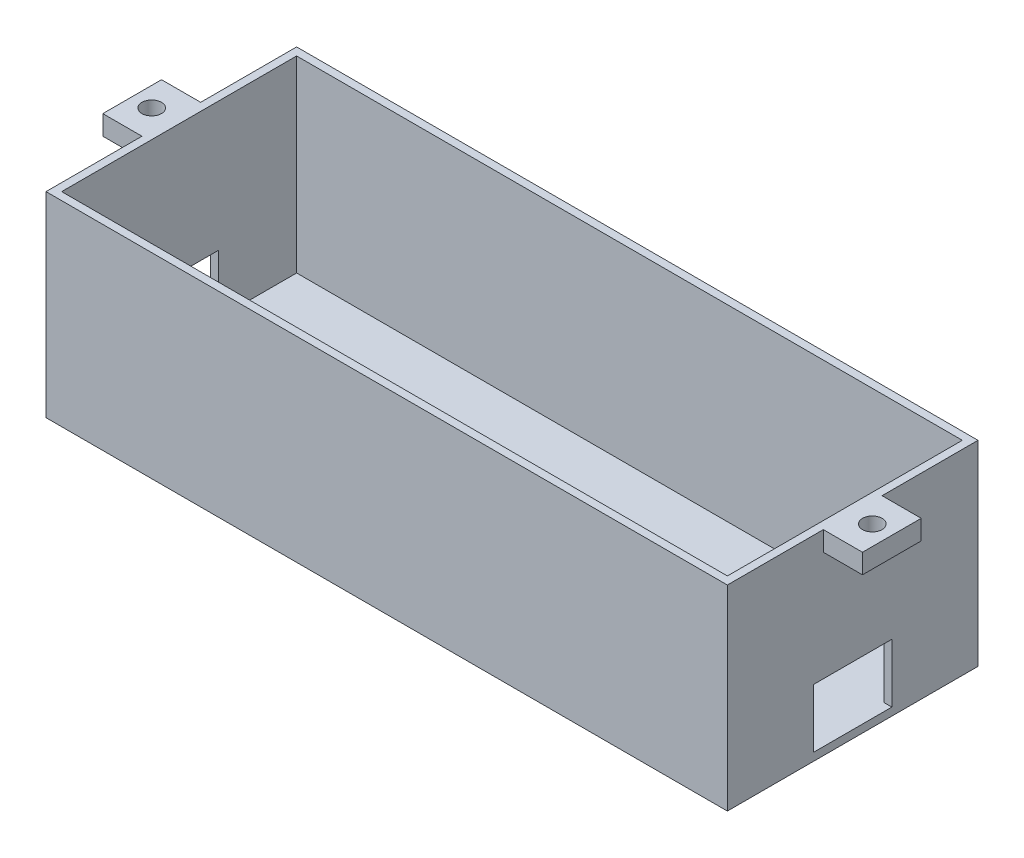
SolidWorks part; units mm, degrees
ref_plane "Front Plane" through (0, 0, 0) normal (0, 0, 1) x (1, 0, 0)
ref_plane "Top Plane" through (0, 0, 0) normal (0, 1, 0) x (1, 0, 0)
ref_plane "Right Plane" through (0, 0, 0) normal (1, 0, 0) x (0, 0, -1)
sketch "Sketch1" plane through (0, 0, 0) normal (0, 1, 0) x (1, 0, 0)
  line L1 (-85, -30) -> (85, -30)
  line L2 (-85, -30) -> (-85, 30)
  line L3 (-85, 30) -> (85, 30)
  line L4 (85, -30) -> (85, 30)
  line L5 (-85, -30) -> (85, 30) construction
  line L6 (-85, 30) -> (85, -30) construction
  line L7 (-87, -32) -> (87, -32)
  line L8 (-87, -32) -> (-87, 32)
  line L9 (-87, 32) -> (87, 32)
  line L10 (87, -32) -> (87, 32)
  line L11 (-87, -32) -> (87, 32) construction
  line L12 (-87, 32) -> (87, -32) construction
  point P0 (0, 0)
  point P6 (0, 0)
  dimension "D1" = 170
  dimension "D2" = 60
  dimension "D3" = 2
  dimension "D4" = 2
extrude "Boss-Extrude1" add sketch "Sketch1" along normal mid plane 50
sketch "Sketch2" plane through (0, 0, -32) normal (0, 0, -1) x (-1, 0, 0)
  line L0 (87, 25) -> (87, -25) construction
  line L1 (-87, -25) -> (87, -25)
  line L2 (-87, -25) -> (-87, -23)
  line L3 (-87, -23) -> (87, -23)
  line L4 (87, -25) -> (87, -23)
  dimension "D1" = 2
extrude "Boss-Extrude2" add sketch "Sketch2" against normal up to surface (64 mm away) up to face at (0, 0, 32)
sketch "Sketch9" plane through (0, 25, 0) normal (0, 1, 0) x (1, 0, 0)
  line L0 (-87, 32) -> (-87, -32) construction
  line L1 (-87, 7.5) -> (-97, 7.5)
  line L2 (-87, 7.5) -> (-87, -7.5)
  line L3 (-87, -7.5) -> (-97, -7.5)
  line L4 (-97, 7.5) -> (-97, -7.5)
  line L5 (0, 30) -> (0, -30)
  line L6 (85, 30) -> (-85, 30) construction
  line L7 (-85, -30) -> (85, -30) construction
  line L13 (87, -7.5) -> (97, -7.5)
  line L14 (97, 7.5) -> (97, -7.5)
  line L15 (-97, 7.5) -> (-87, 7.5)
  line L16 (-97, 7.5) -> (-97, -7.5)
  line L17 (-97, -7.5) -> (-87, -7.5)
  line L18 (-87, 7.5) -> (-87, -7.5)
  line L19 (87, 7.5) -> (97, 7.5)
  line L20 (87, 7.5) -> (87, -7.5)
  circle A0 centre (-92, 0) radius 2.5
  circle A1 centre (92, 0) radius 2.5
  point P6 (-87, 0)
  point P21 (-92, -7.5)
  dimension "D3" = 5
  dimension "D1" = 10
  dimension "D2" = 15
extrude "Boss-Extrude3" add sketch "Sketch9" against normal blind 5
sketch "Sketch10" plane through (-87, 0, 0) normal (-1, 0, 0) x (0, 0, 1)
  line L1 (-10, -23) -> (10, -23)
  line L2 (-10, -23) -> (-10, -8)
  line L3 (-10, -8) -> (10, -8)
  line L4 (10, -23) -> (10, -8)
  line L5 (-32, -25) -> (32, -25) construction
  point P6 (0, -23)
  dimension "D1" = 20
  dimension "D2" = 15
  dimension "D3" = 2
extrude "Cut-Extrude2" cut sketch "Sketch10" against normal up to surface (174 mm away) up to face at (87, 11.25, 0)
sketch "Sketch11" plane through (0, -23, 0) normal (0, 1, 0) x (1, 0, 0)
  line L0 (-41.5, 30) -> (-41.5, -30)
  line L1 (85, 30) -> (-85, 30) construction
  line L2 (-85, -30) -> (85, -30) construction
  line L3 (-85, 30) -> (-85, 10) construction
  circle A0 centre (0, 0) radius 2.5
  circle A1 centre (-41.5, 14) radius 1.25
  circle A2 centre (-41.5, -14) radius 1.25
  point P0 (0, 0)
  point P10 (-41.5, 14)
  point P11 (-41.5, -14)
  dimension "D4" = 5
  dimension "D5" = 2.5
  dimension "D1" = 43.5
  dimension "D2" = 16
  dimension "D3" = 16
extrude "Cut-Extrude3" cut sketch "Sketch11" against normal up to next contours A1 | A2 | A0
